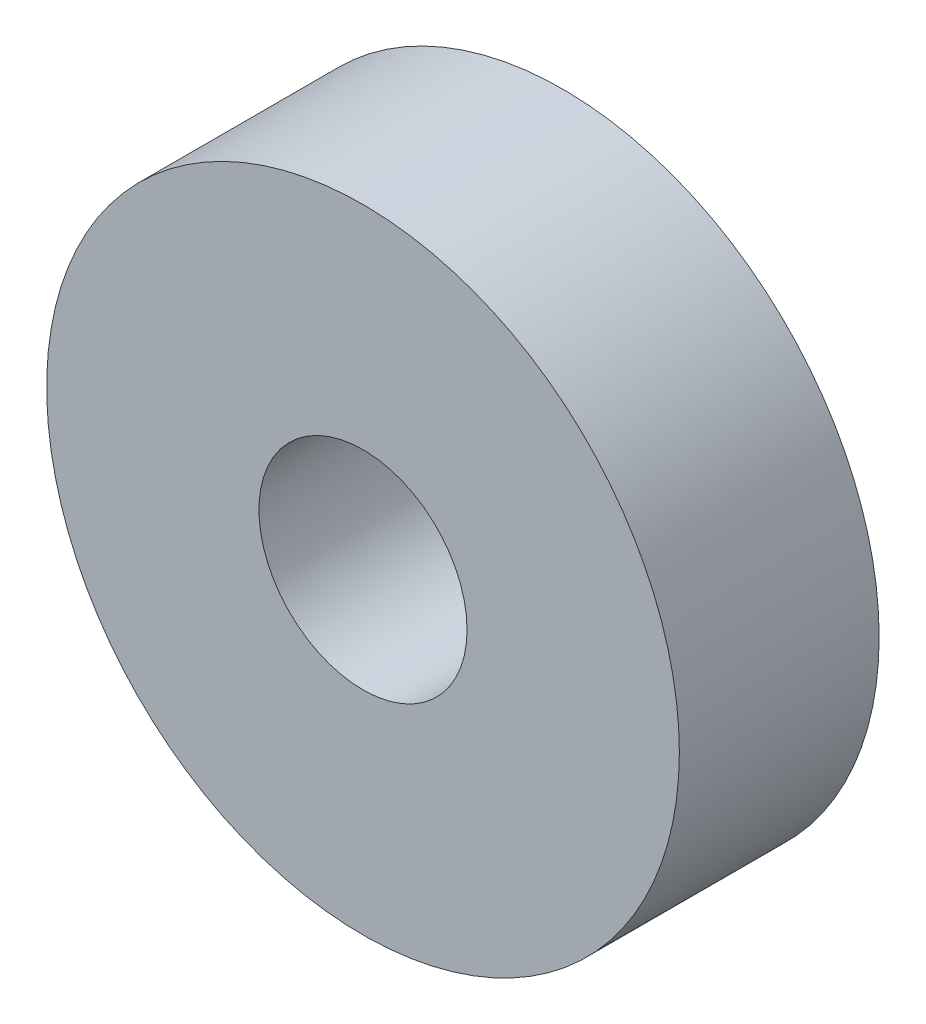
SolidWorks part; units mm, degrees
material "Chrome Stainless Steel"
ref_plane "Front Plane" through (0, 0, 0) normal (0, 0, 1) x (1, 0, 0)
ref_plane "Top Plane" through (0, 0, 0) normal (0, 1, 0) x (1, 0, 0)
ref_plane "Right Plane" through (0, 0, 0) normal (1, 0, 0) x (0, 0, -1)
sketch "Sketch1" plane through (0, 0, 0) normal (0, 0, 1) x (1, 0, 0)
  circle A0 centre (0, 0) radius 3.125
  circle A1 centre (0, 0) radius 9.5
  dimension "D1" = 6.25
  dimension "D2" = 19
extrude "Boss-Extrude1" add sketch "Sketch1" along normal blind 6
